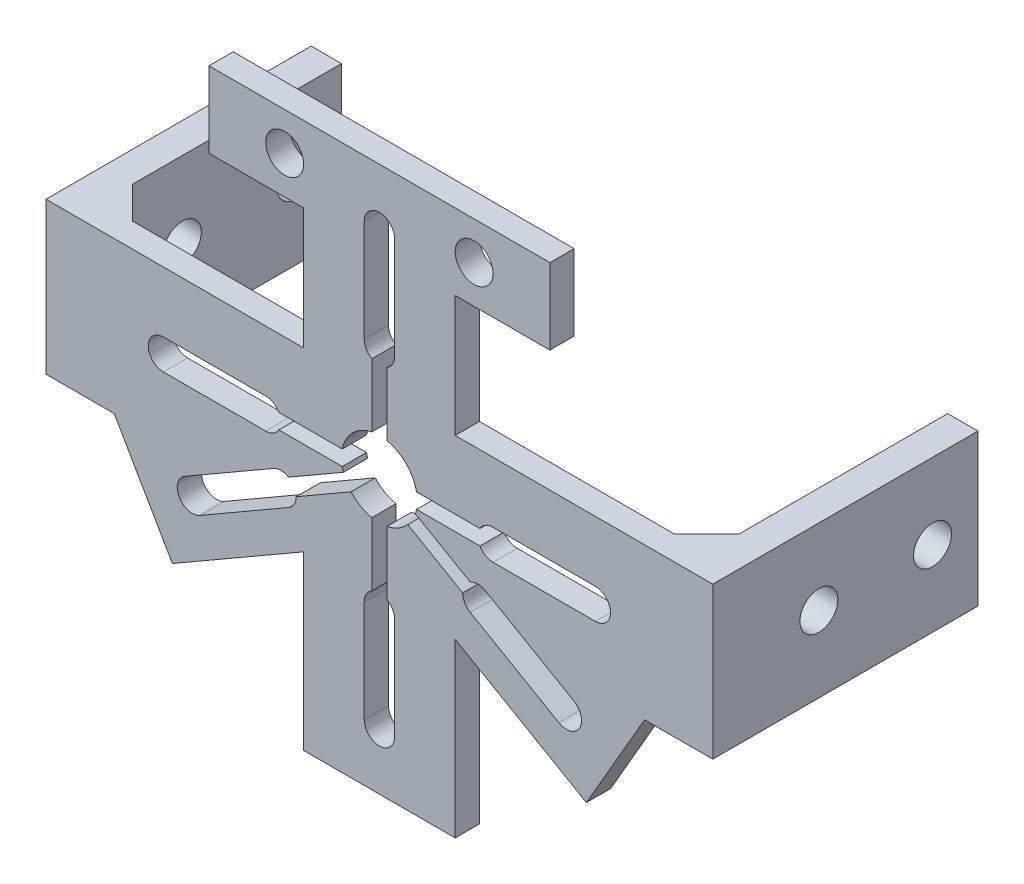
SolidWorks part; units mm, degrees
ref_plane "Front Plane" through (0, 0, 0) normal (0, 0, 1) x (1, 0, 0)
ref_plane "Top Plane" through (0, 0, 0) normal (0, 1, 0) x (1, 0, 0)
ref_plane "Right Plane" through (0, 0, 0) normal (1, 0, 0) x (0, 0, -1)
sketch "Sketch1" plane through (0, 0, 0) normal (0, 0, 1) x (1, 0, 0)
  line L0 (0, 36) -> (0, -36) construction
  line L1 (22.5, 36) -> (-22.5, 36)
  line L2 (-22.5, 36) -> (-22.5, 26)
  line L3 (-22.5, 26) -> (-10, 26)
  line L4 (-10, 26) -> (-10, 10)
  line L5 (-10, 10) -> (-40, 10)
  line L6 (-40, 10) -> (-40, -10)
  line L7 (-40, -10) -> (-35, -10)
  line L8 (-35, -10) -> (-27.3205, -23.3013)
  line L9 (-27.3205, -23.3013) -> (-10, -13.3013)
  line L10 (-10, -13.3013) -> (-10, -36)
  line L11 (-10, -36) -> (10, -36)
  line L12 (0, 28.5) -> (0, 15) construction
  line L13 (2, 28.5) -> (2, 15)
  line L14 (-2, 28.5) -> (-2, 15)
  line L15 (-1, 13.2679) -> (-1, 4.899)
  line L16 (1, 13.2679) -> (1, 4.899)
  line L17 (28.5, 2) -> (15, 2)
  line L18 (28.5, -2) -> (15, -2)
  line L19 (13.2679, 1) -> (4.899, 1)
  line L20 (13.2679, -1) -> (4.899, -1)
  line L21 (2, -28.5) -> (2, -15)
  line L22 (-2, -28.5) -> (-2, -15)
  line L23 (1, -13.2679) -> (1, -4.899)
  line L24 (-1, -13.2679) -> (-1, -4.899)
  line L25 (-28.5, -2) -> (-15, -2)
  line L26 (-28.5, 2) -> (-15, 2)
  line L27 (-13.2679, -1) -> (-4.899, -1)
  line L28 (-13.2679, 1) -> (-4.899, 1)
  line L29 (23.6817, -15.9821) -> (11.9904, -9.2321)
  line L30 (25.6817, -12.5179) -> (13.9904, -5.7679)
  line L31 (10.9904, -7.5) -> (3.7426, -3.3155)
  line L32 (11.9904, -5.7679) -> (4.7426, -1.5835)
  line L33 (-25.6817, -12.5179) -> (-13.9904, -5.7679)
  line L34 (-23.6817, -15.9821) -> (-11.9904, -9.2321)
  line L35 (-11.9904, -5.7679) -> (-4.7426, -1.5835)
  line L36 (-10.9904, -7.5) -> (-3.7426, -3.3155)
  line L37 (10, -13.3013) -> (10, -36)
  line L38 (27.3205, -23.3013) -> (10, -13.3013)
  line L39 (35, -10) -> (27.3205, -23.3013)
  line L40 (40, -10) -> (35, -10)
  line L41 (40, 10) -> (40, -10)
  line L42 (10, 10) -> (40, 10)
  line L43 (10, 26) -> (10, 10)
  line L44 (22.5, 26) -> (10, 26)
  line L45 (22.5, 36) -> (22.5, 26)
  arc A0 (-1, 4.899) -> (-4.899, 1) centre (0, 0) ccw
  arc A1 (2, 28.5) -> (-2, 28.5) centre (0, 28.5) ccw
  arc A2 (-2, 15) -> (-1, 13.2679) centre (0, 15) ccw
  arc A3 (1, 13.2679) -> (2, 15) centre (0, 15) ccw
  arc A4 (28.5, -2) -> (28.5, 2) centre (28.5, 0) ccw
  arc A5 (13.2679, -1) -> (15, -2) centre (15, 0) ccw
  arc A6 (15, 2) -> (13.2679, 1) centre (15, 0) ccw
  arc A7 (-2, -28.5) -> (2, -28.5) centre (0, -28.5) ccw
  arc A8 (-1, -13.2679) -> (-2, -15) centre (0, -15) ccw
  arc A9 (2, -15) -> (1, -13.2679) centre (0, -15) ccw
  arc A10 (-28.5, 2) -> (-28.5, -2) centre (-28.5, 0) ccw
  arc A11 (-13.2679, 1) -> (-15, 2) centre (-15, 0) ccw
  arc A12 (-15, -2) -> (-13.2679, -1) centre (-15, 0) ccw
  arc A13 (23.6817, -15.9821) -> (25.6817, -12.5179) centre (24.6817, -14.25) ccw
  arc A14 (13.9904, -5.7679) -> (11.9904, -5.7679) centre (12.9904, -7.5) ccw
  arc A15 (10.9904, -7.5) -> (11.9904, -9.2321) centre (12.9904, -7.5) ccw
  arc A16 (-25.6817, -12.5179) -> (-23.6817, -15.9821) centre (-24.6817, -14.25) ccw
  arc A17 (-11.9904, -9.2321) -> (-10.9904, -7.5) centre (-12.9904, -7.5) ccw
  arc A18 (-11.9904, -5.7679) -> (-13.9904, -5.7679) centre (-12.9904, -7.5) ccw
  arc A19 (-3.7426, -3.3155) -> (-1, -4.899) centre (0, 0) ccw
  arc A20 (-4.899, -1) -> (-4.7426, -1.5835) centre (0, 0) ccw
  arc A21 (4.899, 1) -> (1, 4.899) centre (0, 0) ccw
  arc A22 (4.7426, -1.5835) -> (4.899, -1) centre (0, 0) ccw
  arc A23 (1, -4.899) -> (3.7426, -3.3155) centre (0, 0) ccw
  point P3 (0, 0)
  point P5 (-25.6817, -19.6045)
  point P18 (0, 21.75)
  point P23 (-10, 18)
  point P29 (-35.6958, -1.2251)
  point P61 (0, 0)
  point P81 (0, 0)
  point P91 (0, 0)
  point P92 (-40, 0)
  dimension "D2" = 10
  dimension "D9" = 15
  dimension "D11" = 2
  dimension "D12" = 2
  dimension "D13" = 2
  dimension "D15" = 28.5
  dimension "D18" = 20
  dimension "D1" = 72
  dimension "D3" = 13.5
  dimension "D4" = 4
  dimension "D5" = 10
  dimension "D6" = 10
  dimension "D7" = 22.5
  dimension "D8" = 40
  dimension "D10" = 5
  dimension "D14" = 13.5
  dimension "D19" = 20
  dimension "D16" = 4
  dimension "D17" = 3
extrude "Boss-Extrude1" add sketch "Sketch1" along normal blind 3.2
sketch "Sketch2" plane through (0, 0, 3.2) normal (0, 0, -1) x (-1, 0, 0)
  line L0 (0, 9.796) -> (0, -7.5899) construction
  line L9 (40, -10) -> (44, -10)
  line L10 (-40, 10) -> (-44, 10)
  line L11 (-40, 10) -> (-40, -10)
  line L12 (-40, -10) -> (-44, -10)
  line L13 (-44, 10) -> (-44, -10)
  line L14 (44, 10) -> (44, -10)
  line L15 (40, 10) -> (44, 10)
  line L16 (40, 10) -> (40, -10)
  dimension "D1" = 4
  dimension "D2" = 20
extrude "Boss-Extrude2" add sketch "Sketch2" along normal blind 35
sketch "Sketch3" plane through (0, 10, 0) normal (0, 1, 0) x (1, 0, 0)
  line L5 (0, 7.9938) -> (0, -7.5857) construction
  line L11 (-40, 4.2426) -> (-35.7574, 0)
  line L12 (-40, 31.8) -> (-40, 0) construction
  line L13 (-35.7574, 0) -> (-40, 0)
  line L14 (-40, 0) -> (-40, 4.2426)
  line L15 (35.7574, 0) -> (40, 0)
  line L16 (40, 0) -> (40, 4.2426)
  line L17 (40, 4.2426) -> (35.7574, 0)
  dimension "D1" = 6
  dimension "D2" = 45
extrude "Boss-Extrude3" add sketch "Sketch3" against normal up to surface (20 mm away) up to face at (-39.6667, -10, -9.5333)
sketch "Sketch4" plane through (-44, 0, 0) normal (-1, 0, 0) x (0, 0, 1)
  line L0 (-31.8, -10) -> (-31.8, 10) construction
  circle A0 centre (-25.8, 0) radius 2.5
  circle A1 centre (-10.8, 0) radius 2.5
  point P6 (0, 0)
  dimension "D1" = 5
  dimension "D2" = 6
  dimension "D3" = 15
extrude "Cut-Extrude1" cut sketch "Sketch4" against normal up to surface (88 mm away) up to face at (44, 0, -14.3)
sketch "Sketch5" plane through (0, 0, 3.2) normal (0, 0, 1) x (1, 0, 0)
  line L0 (-22.5, 36) -> (-22.5, 26) construction
  line L1 (-22.5, 36) -> (-22.5, 26) construction
  line L2 (-22.5, 26) -> (-10, 26) construction
  line L3 (0, 0) -> (0, 40.8494) construction
  circle A0 centre (-12.5, 31) radius 2.5
  circle A1 centre (12.5, 31) radius 2.5
  point P11 (-22.5, 31)
  dimension "D1" = 5
  dimension "D2" = 12.5
extrude "Cut-Extrude2" cut sketch "Sketch5" against normal up to surface (3.2 mm away) up to face at (0, 1.5397, 0)
